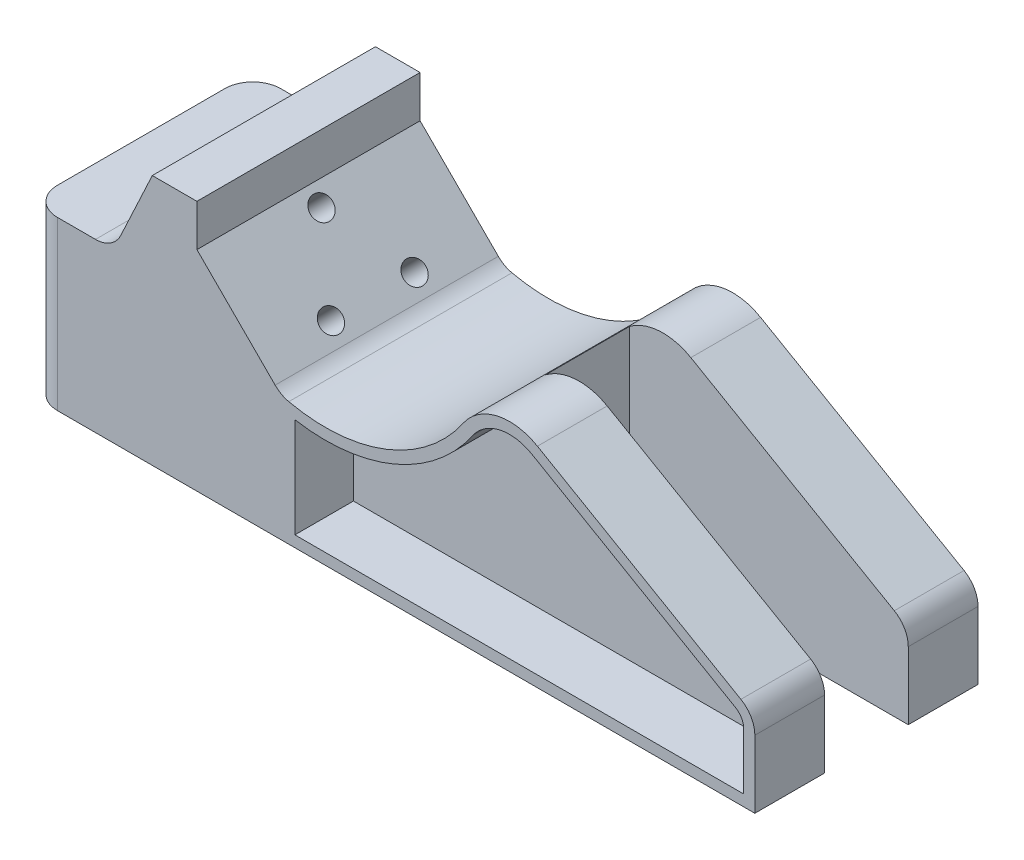
SolidWorks part; units mm, degrees
material "AISI 304"
ref_plane "Front Plane" through (0, 0, 0) normal (0, 0, 1) x (1, 0, 0)
ref_plane "Top Plane" through (0, 0, 0) normal (0, 1, 0) x (1, 0, 0)
ref_plane "Right Plane" through (0, 0, 0) normal (1, 0, 0) x (0, 0, -1)
sketch "Sketch2" plane through (0, 0, 0) normal (0, 0, 1) x (1, 0, 0)
  line L0 (0, 0) -> (-130, 0)
  line L1 (-130, 0) -> (-130, 30)
  line L2 (-130, 30) -> (-118.1854, 30)
  line L3 (-113.6538, 32.8869) -> (-108.0054, 45)
  line L4 (-108.0054, 45) -> (-100.0054, 45)
  line L5 (-100.0054, 45) -> (-100.0054, 37.5)
  line L6 (-100.0054, 37.5) -> (-85.9823, 23.4769)
  line L7 (-38.9711, 37.5) -> (-2.5, 16.4434)
  line L8 (0, 12.1132) -> (0, 0)
  arc A0 (-83.5372, 22.1328) -> (-52.227, 34.4825) centre (-76.9947, 51.4107) ccw
  arc A1 (-52.227, 34.4825) -> (-38.9711, 37.5) centre (-43.9711, 28.8397) cw
  arc A2 (-85.9823, 23.4769) -> (-83.5372, 22.1328) centre (-82.4468, 27.0124) ccw
  arc A3 (-2.5, 16.4434) -> (0, 12.1132) centre (-5, 12.1132) cw
  arc A5 (-113.6538, 32.8869) -> (-118.1854, 30) centre (-118.1854, 35) cw
  point P5 (-115, 30)
  point P14 (-115, 15)
  point P15 (-103.0228, 73.2662)
  point P16 (-97.0023, 28.4865)
  point P17 (-92.186, 17.5769)
  point P18 (-92.186, 29.7027)
  point P19 (-82.2522, 19.65)
  point P20 (-93.9921, 24.5005)
  point P21 (-76.8338, 15)
  point P22 (-99.7115, 22.6943)
  point P23 (-110.8494, 52.1946)
  point P24 (-100.2797, 38.3721)
  point P25 (-95.4972, 30)
  point P26 (-105.0325, 66.4052)
  point P27 (-73.7181, 46.7056)
  point P28 (-96.7181, 69.2056)
  point P29 (-73.7181, 46.7056)
  point P30 (-79.5047, 34.2963)
  point P33 (-85.0054, 22.5)
  point P36 (0, 15)
  point P39 (-115, 30)
  point P40 (-116.6619, 30)
  point P42 (-115, 30)
  point P43 (-52.227, 35)
  point P44 (-38.9711, 37.5)
  point P45 (-52.227, 35)
  point P46 (-53.1249, 32.8869)
  point P47 (-53.0142, 32.8869)
  dimension "D6" = 10
  dimension "D9" = 30
  dimension "D15" = 5
  dimension "D16" = 5
  dimension "D17" = 5
  dimension "D1" = 30
  dimension "D2" = 15
  dimension "D3" = 130
  dimension "D4" = 15
  dimension "D5" = 8
  dimension "D7" = 45
  dimension "D8" = 60
  dimension "D10" = 7.5
  dimension "D11" = 15
  dimension "D12" = 15
  dimension "D13" = 65
  dimension "D14" = 15
extrude "Boss-Extrude1" add sketch "Sketch2" along normal mid plane 40
sketch "Sketch4" plane through (0, 0, 0) normal (0, 0, 1) x (1, 0, 0)
  line L0 (0, 0) -> (0, 12.1132) construction
  line L1 (-50, 67.5637) -> (13.5149, 67.5637)
  line L2 (-50, 67.5637) -> (-50, -36.0473)
  line L3 (-50, -36.0473) -> (13.5149, -36.0473)
  line L4 (13.5149, 67.5637) -> (13.5149, -36.0473)
  dimension "D1" = 50
extrude "Cut-Extrude2" cut sketch "Sketch4" against normal mid plane 15
sketch "Sketch6" plane through (-31.2527, -31.2527, 0) normal (0.7071, 0.7071, 0) x (0, 0, -1)
  line L0 (-20, 97.231) -> (20, 97.231) construction
  circle A0 centre (0, 93.931) radius 2
  circle A1 centre (-7.5, 80.9406) radius 2
  circle A2 centre (7.5, 80.9406) radius 2
  point P6 (0, 0)
  point P10 (0, 0)
  point P11 (0, 0)
  point P12 (0, 0)
  dimension "D1" = 4
  dimension "D2" = 4
  dimension "D3" = 4
  dimension "D4" = 3.3
  dimension "D5" = 15
  dimension "D6" = 15
  dimension "D7" = 15
sketch "Sketch7" plane through (0, 0, 20) normal (0, 0, 1) x (1, 0, 0)
  line L0 (-82.4468, 2) -> (-82.4468, 19.8786)
  line L18 (-2, 2) -> (-2, 12.1132)
  line L19 (-3.5, 14.7113) -> (-39.9711, 35.7679)
  line L20 (-87.3965, 22.0627) -> (-102.0054, 36.6716)
  line L21 (-102.0054, 36.6716) -> (-102.0054, 43)
  line L22 (-102.0054, 43) -> (-106.7312, 43)
  line L23 (-106.7312, 43) -> (-111.8412, 32.0417)
  line L24 (-118.1854, 28) -> (-128, 28)
  line L25 (-128, 28) -> (-128, 2)
  line L26 (-128, 2) -> (-2, 2)
  line L27 (-2, 2) -> (-2, 12.1132)
  line L28 (-3.5, 14.7113) -> (-39.9711, 35.7679)
  line L35 (-82.4468, 2) -> (-2, 2)
  arc A10 (-2, 12.1132) -> (-3.5, 14.7113) centre (-5, 12.1132) ccw
  arc A11 (-39.9711, 35.7679) -> (-50.5758, 33.3539) centre (-43.9711, 28.8397) ccw
  arc A12 (-83.9734, 20.1809) -> (-50.5758, 33.3539) centre (-76.9947, 51.4107) ccw
  arc A13 (-87.3965, 22.0627) -> (-83.9734, 20.1809) centre (-82.4468, 27.0124) ccw
  arc A14 (-118.1854, 28) -> (-111.8412, 32.0417) centre (-118.1854, 35) ccw
  arc A15 (-2, 12.1132) -> (-3.5, 14.7113) centre (-5, 12.1132) ccw
  arc A16 (-39.9711, 35.7679) -> (-50.5758, 33.3539) centre (-43.9711, 28.8397) ccw
  arc A17 (-82.4468, 19.8786) -> (-50.5758, 33.3539) centre (-76.9947, 51.4107) ccw
  dimension "D1" = 2
extrude "Cut-Extrude6" cut sketch "Sketch7" against normal offset from surface (10.5 mm away) 2 up to face at (-23.499, 17.4785, 7.5)
fillet "Fillet1" radius 5 2 edges at (-130, 15, -20) (-130, 15, 20)
sketch "Sketch8" plane through (-31.2527, -31.2527, 0) normal (0.7071, 0.7071, 0) x (0, 0, -1)
  line L1 (-20, 97.231) -> (20, 97.231) construction
  circle A0 centre (0, 93.931) radius 2
  circle A1 centre (-7.5, 80.9406) radius 2
  circle A2 centre (7.5, 80.9406) radius 2
  point P6 (0, 0)
  point P10 (0, 97.231)
  dimension "D1" = 4
  dimension "D2" = 4
  dimension "D3" = 4
  dimension "D4" = 15
  dimension "D5" = 15
  dimension "D6" = 15
  dimension "D7" = 3.3
extrude "Cut-Extrude7" cut sketch "Sketch8" against normal blind 25
extrude "Cut-Extrude4" cut sketch "Sketch6" against normal blind 25
